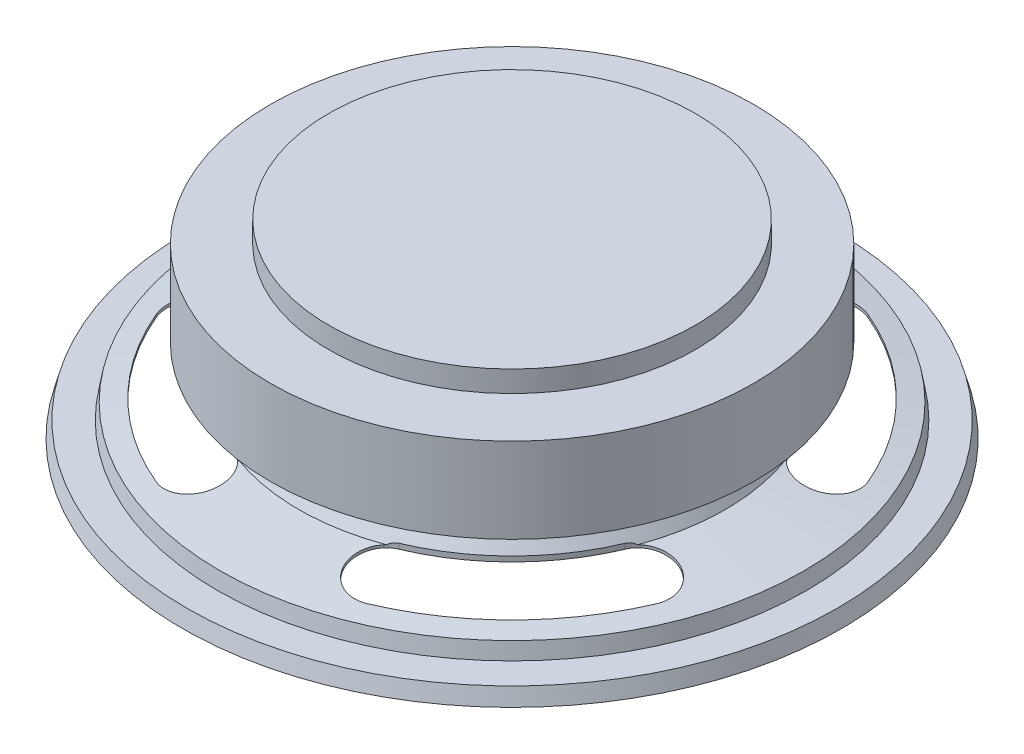
SolidWorks part; units mm, degrees
ref_plane "Front Plane" through (0, 0, 0) normal (0, 0, 1) x (1, 0, 0)
ref_plane "Top Plane" through (0, 0, 0) normal (0, 1, 0) x (1, 0, 0)
ref_plane "Right Plane" through (0, 0, 0) normal (1, 0, 0) x (0, 0, -1)
sketch "Sketch2" plane through (0, 0, 0) normal (0, 0, 1) x (1, 0, 0)
  line L0 (0, 0) -> (0, 73.6548) construction
  line L1 (0, 0) -> (0, -76.5256) construction
  line L2 (0, 0) -> (-24.6063, 0) construction
  line L3 (-24.6063, 0) -> (-24.2936, 1.1669)
  line L4 (-24.2936, 1.1669) -> (-24.2936, 0) construction
  line L5 (-24.2936, 1.1669) -> (-22.0048, 1.1669)
  line L6 (-22.0048, 1.1669) -> (-21.7991, 2.3339)
  line L7 (-22.0048, 1.1669) -> (-21.7991, 1.1669) construction
  line L8 (-21.7991, 2.3339) -> (-21.7991, 1.1669) construction
  line L9 (-21.7991, 2.3339) -> (-15.9364, 3.3676)
  line L10 (-21.7991, 2.3339) -> (-15.9364, 2.3339) construction
  line L11 (-15.9364, 2.3339) -> (-15.9364, 3.3676) construction
  line L12 (-15.9364, 3.3676) -> (-15.2032, 3.3676) construction
  line L13 (-15.2032, 3.3676) -> (-15.2032, 4.6376) construction
  line L14 (-15.9364, 3.3676) -> (-15.2032, 4.6376)
  line L15 (0, 14.1626) -> (-13.6922, 14.1626)
  line L16 (-13.6922, 14.1626) -> (-13.6922, 4.6376)
  line L17 (-13.6922, 4.6376) -> (-15.2032, 4.6376)
  dimension "D1" = 24.6062
  dimension "D2" = 75
  dimension "D3" = 5.9531
  dimension "D4" = 1.1669
  dimension "D5" = 80
  dimension "D6" = 1.27
  dimension "D7" = 10
  dimension "D10" = 60
  dimension "D11" = 13.6922
  dimension "D12" = 9.525
revolve "Revolve-Thin1" add sketch "Sketch2" angle 360 about L0
sketch "Sketch4" plane through (0, 0, 0) normal (0, 1, 0) x (1, 0, 0)
  line L0 (-11.1847, -11.1847) -> (0, 0) construction
  line L1 (0, 0) -> (0, -24.6063) construction
  line L3 (-12.7653, -12.7653) -> (-14.346, -14.346) construction
  line L4 (-14.346, -14.346) -> (-17.3992, -17.3992) construction
  line L5 (-12.7653, -12.7653) -> (-11.1847, -11.1847) construction
  line L6 (-4.7625, -16.6415) -> (4.7625, -16.6415) construction
  arc A0 (-16.6415, -6.9978) -> (-6.9978, -16.6415) centre (0, 0) ccw construction
  arc A1 (-18.702, -7.8643) -> (-7.8643, -18.702) centre (0, 0) ccw
  arc A2 (-14.5809, -6.1313) -> (-6.1313, -14.5809) centre (0, 0) ccw
  arc A3 (-14.5809, -6.1313) -> (-18.702, -7.8643) centre (-16.6415, -6.9978) ccw
  arc A4 (-7.8643, -18.702) -> (-6.1313, -14.5809) centre (-6.9978, -16.6415) ccw
  circle A5 centre (0, 0) radius 24.6063 construction
  arc A6 (-6.9978, 16.6415) -> (-16.6415, 6.9978) centre (0, 0) ccw construction
  arc A7 (-7.8643, 18.702) -> (-18.702, 7.8643) centre (0, 0) ccw
  arc A8 (-6.1313, 14.5809) -> (-14.5809, 6.1313) centre (0, 0) ccw
  arc A9 (-6.1313, 14.5809) -> (-7.8643, 18.702) centre (-6.9978, 16.6415) ccw
  arc A10 (-18.702, 7.8643) -> (-14.5809, 6.1313) centre (-16.6415, 6.9978) ccw
  arc A11 (16.6415, 6.9978) -> (6.9978, 16.6415) centre (0, 0) ccw construction
  arc A12 (18.702, 7.8643) -> (7.8643, 18.702) centre (0, 0) ccw
  arc A13 (14.5809, 6.1313) -> (6.1313, 14.5809) centre (0, 0) ccw
  arc A14 (14.5809, 6.1313) -> (18.702, 7.8643) centre (16.6415, 6.9978) ccw
  arc A15 (7.8643, 18.702) -> (6.1313, 14.5809) centre (6.9978, 16.6415) ccw
  arc A16 (6.9978, -16.6415) -> (16.6415, -6.9978) centre (0, 0) ccw construction
  arc A17 (7.8643, -18.702) -> (18.702, -7.8643) centre (0, 0) ccw
  arc A18 (6.1313, -14.5809) -> (14.5809, -6.1313) centre (0, 0) ccw
  arc A19 (6.1313, -14.5809) -> (7.8643, -18.702) centre (6.9978, -16.6415) ccw
  arc A20 (18.702, -7.8643) -> (14.5809, -6.1313) centre (16.6415, -6.9978) ccw
  circle A22 centre (0, 0) radius 15.9364 construction
  circle A23 centre (0, 0) radius 15.9364 construction
  point P4 (-12.7653, -12.7653)
  point P20 (-12.7653, 12.7653)
  point P27 (12.7653, 12.7653)
  point P34 (12.7653, -12.7653)
  point P39 (0, 0)
  point P40 (0, 0)
  dimension "D1" = 45
  dimension "D4" = 9.525
  dimension "D2" = 4
extrude "Cut-Extrude2" cut sketch "Sketch4" along normal through all
sketch "Sketch5" plane through (0, 0, 0) normal (0, 0, 1) x (1, 0, 0)
  line L4 (0, 14.1626) -> (-13.6922, 14.1626) construction
  line L5 (-13.6922, 14.1626) -> (-13.6922, 4.6376) construction
  line L6 (-13.6922, 4.6376) -> (-15.2032, 4.6376) construction
  line L7 (-15.9364, 3.3676) -> (-15.2032, 4.6376) construction
  line L8 (-21.7991, 2.3339) -> (-15.9364, 3.3676) construction
  line L9 (-22.0048, 1.1669) -> (-21.7991, 2.3339) construction
  line L10 (-24.2936, 1.1669) -> (-22.0048, 1.1669) construction
  line L11 (-24.6063, 0) -> (-24.2936, 1.1669) construction
  line L12 (0, 14.1626) -> (-13.6922, 14.1626)
  line L13 (-13.6922, 14.1626) -> (-13.6922, 4.6376)
  line L14 (-13.6922, 4.6376) -> (-15.2032, 4.6376)
  line L15 (-15.9364, 3.3676) -> (-15.2032, 4.6376)
  line L16 (-21.7991, 2.3339) -> (-15.9364, 3.3676)
  line L17 (-22.0048, 1.1669) -> (-21.7991, 2.3339)
  line L18 (-24.2936, 1.1669) -> (-22.0048, 1.1669)
  line L19 (-24.6063, 0) -> (-24.2936, 1.1669)
  line L21 (-13.6922, 12.5751) -> (-18.0422, 12.5751)
  line L22 (-13.6922, 12.5751) -> (-13.6922, 6.2251)
  line L23 (-13.6922, 6.2251) -> (-18.0422, 6.2251)
  line L24 (-18.0422, 12.5751) -> (-18.0422, 6.2251)
  dimension "D1" = 6.35
  dimension "D2" = 1.5875
  dimension "D3" = 4.35
revolve "Revolve1" add sketch "Sketch5" angle 360 about L0
sketch "Sketch6" plane through (0, 4.4392, 0) normal (0, -1, 0) x (1, 0, 0)
  circle A0 centre (0, 0) radius 1.5875
  dimension "D1" = 3.175
extrude "Boss-Extrude2" add sketch "Sketch6" against normal up to surface (9.525 mm away) and the other way blind 1 up to face at (0, 13.9642, -13.4937)
sketch "Sketch7" plane through (0, 0, 0) normal (0, 0, 1) x (1, 0, 0)
  line L0 (-1.5875, 3.4392) -> (-3.402, 2.6421)
  line L1 (-1.5875, 3.4392) -> (1.5875, 3.4392) construction
  line L2 (-3.402, 2.6421) -> (-3.402, 3.4392)
  line L3 (-3.402, 3.4392) -> (-4.6905, 3.4392)
  line L4 (-4.6905, 3.4392) -> (-4.6905, 2.6421)
  line L5 (-4.6905, 2.6421) -> (-5.2164, 2.6421)
  line L6 (-5.2164, 2.6421) -> (-5.199, 3.4594)
  line L7 (-5.199, 3.4594) -> (-23.7948, -0.0514)
  line L8 (24.4146, -0.0514) -> (-24.4146, -0.0514) construction
  line L9 (-23.7948, -0.0514) -> (-23.7948, -0.2488)
  line L10 (-23.7948, -0.2488) -> (-24.4146, -0.2488)
  line L11 (-24.4146, -0.2488) -> (-24.4146, -0.0514)
